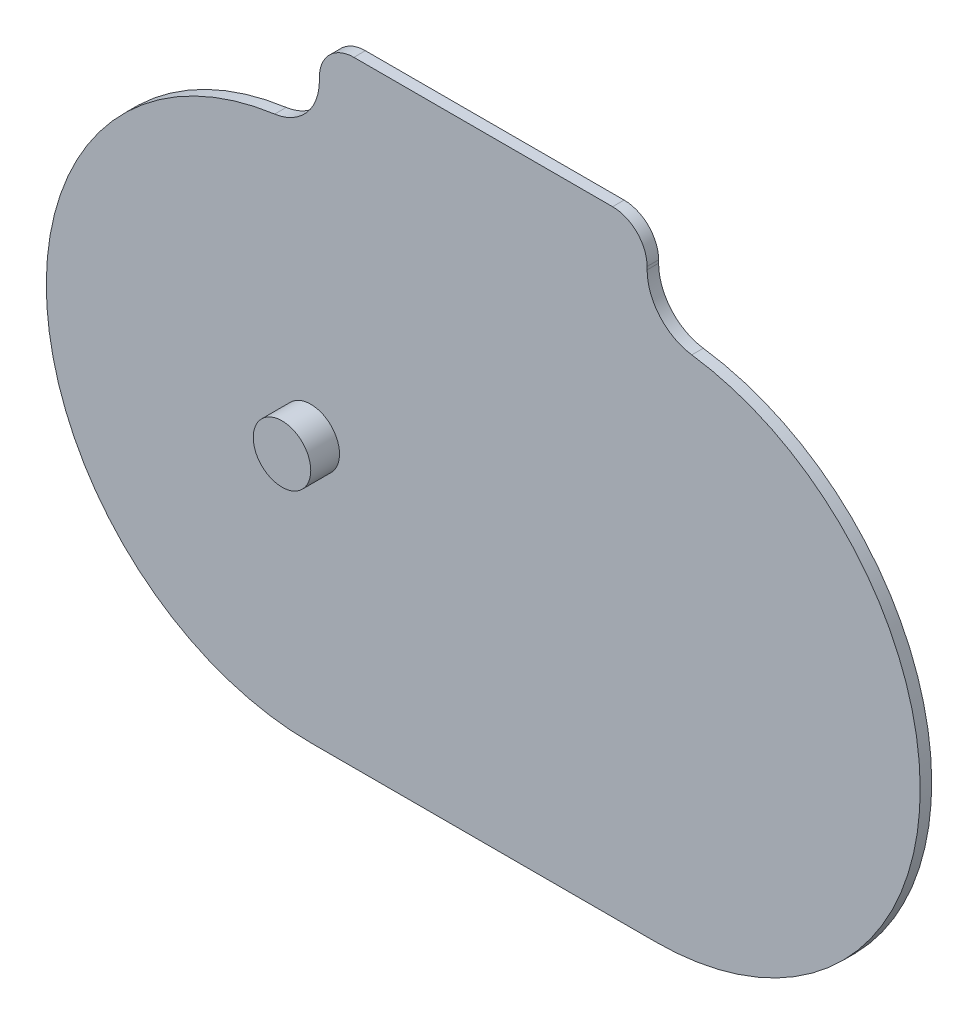
SolidWorks part; units mm, degrees
ref_plane "Front Plane" through (0, 0, 0) normal (0, 0, 1) x (1, 0, 0)
ref_plane "Top Plane" through (0, 0, 0) normal (0, 1, 0) x (1, 0, 0)
ref_plane "Right Plane" through (0, 0, 0) normal (1, 0, 0) x (0, 0, -1)
sketch "Sketch1" plane through (0, 0, 0) normal (0, 0, 1) x (1, 0, 0)
  line L0 (28.5, 54.4862) -> (28.5, 55)
  line L1 (22.5, 61) -> (-22.5, 61)
  line L2 (-28.5, 55) -> (-28.5, 54.4862)
  line L3 (-30, -46) -> (30, -46)
  arc A0 (28.5, 55) -> (22.5, 61) centre (22.5, 55) ccw
  arc A1 (-22.5, 61) -> (-28.5, 55) centre (-22.5, 55) ccw
  arc A2 (-36.2727, 45.5703) -> (-28.5, 54.4862) centre (-37.5, 54.4862) ccw
  arc A3 (-36.2727, 45.5703) -> (-30, -46) centre (-30, 0) ccw
  arc A4 (30, -46) -> (36.2727, 45.5703) centre (30, 0) ccw
  arc A5 (28.5, 54.4862) -> (36.2727, 45.5703) centre (37.5, 54.4862) ccw
extrude "Boss-Extrude1" add sketch "Sketch1" along normal blind 2
sketch "Sketch2" plane through (0, 0, 2) normal (0, 0, 1) x (1, 0, 0)
  line L0 (-76, 0) -> (-30, 0) construction
  arc A0 (-36.2727, 45.5703) -> (-30, -46) centre (-30, 0) ccw construction
  circle A1 centre (-30, 0) radius 5
  dimension "D2" = 10
  dimension "D1" = 46
extrude "Boss-Extrude2" add sketch "Sketch2" along normal blind 5
sketch "Sketch3" plane through (0, 0, 0) normal (0, 0, -1) x (-1, 0, 0)
  line L0 (-76, 0) -> (0, 0) construction
  arc A0 (-36.2727, 45.5703) -> (-30, -46) centre (-30, 0) ccw construction
  circle A1 centre (-30, 0) radius 5
  dimension "D1" = 10
  dimension "D2" = 46
extrude "Boss-Extrude3" add sketch "Sketch3" along normal blind 5
